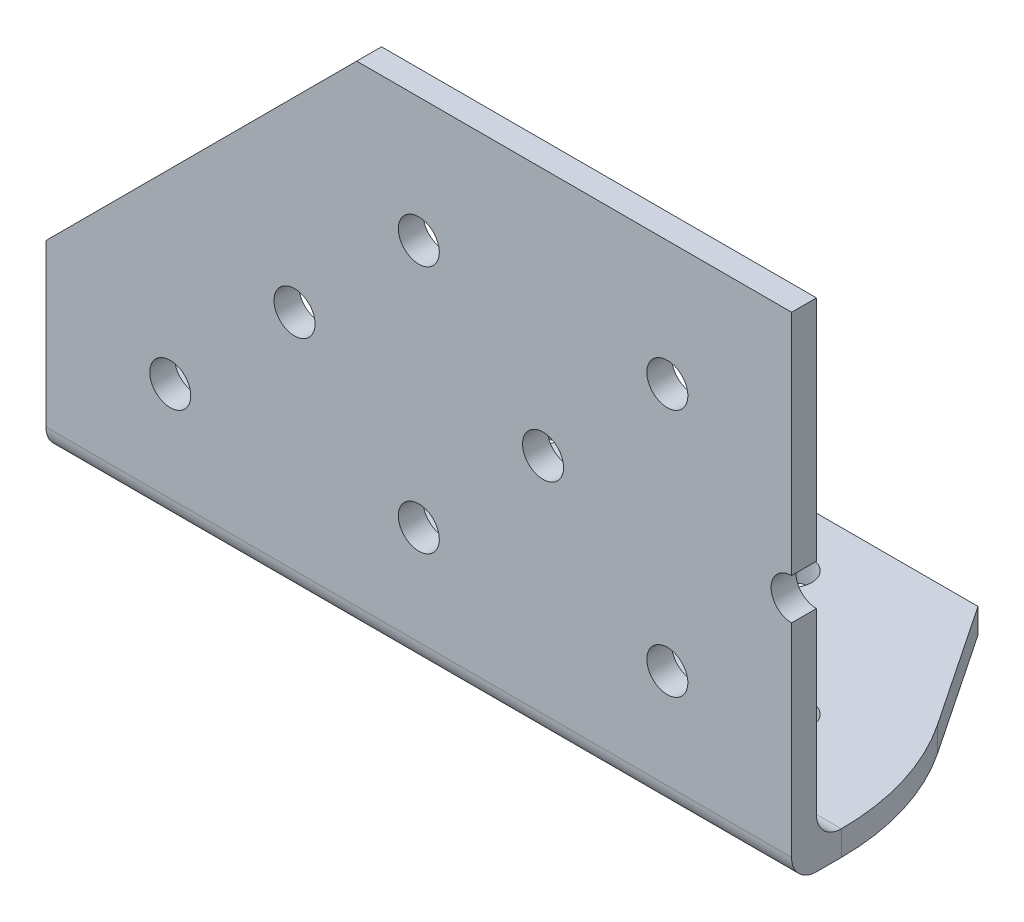
SolidWorks part; units mm, degrees
ref_plane "Front Plane" through (0, 0, 0) normal (0, 0, 1) x (1, 0, 0)
ref_plane "Top Plane" through (0, 0, 0) normal (0, 1, 0) x (1, 0, 0)
ref_plane "Right Plane" through (0, 0, 0) normal (1, 0, 0) x (0, 0, -1)
sketch "Sketch1" plane through (0, 0, 0) normal (1, 0, 0) x (0, 0, -1)
  line L0 (0, 2.54) -> (0, 50.8)
  line L1 (0, 50.8) -> (2.54, 50.8)
  line L2 (2.54, 50.8) -> (2.54, 5.08)
  line L3 (5.08, 2.54) -> (50.8, 2.54)
  line L4 (50.8, 2.54) -> (50.8, 0)
  line L5 (50.8, 0) -> (2.54, 0)
  arc A0 (0, 2.54) -> (2.54, 0) centre (2.54, 2.54) ccw
  arc A1 (5.08, 2.54) -> (2.54, 5.08) centre (5.08, 5.08) cw
  point P10 (0, 0)
  dimension "D5" = 2.54
  dimension "D6" = 2.54
  dimension "D1" = 2.54
  dimension "D2" = 2.54
  dimension "D3" = 50.8
  dimension "D4" = 50.8
extrude "Boss-Extrude1" add sketch "Sketch1" along normal blind 76.2
sketch "Sketch2" plane through (0, 2.54, 0) normal (0, 1, 0) x (1, 0, 0)
  line L0 (76.2, 50.8) -> (0, 50.8) construction
  line L1 (0, 50.8) -> (0, 5.08) construction
  line L2 (12.7, 38.0619) -> (12.7, 12.6619) construction
  line L3 (0, 25.3619) -> (5.5771, 25.3619) construction
  circle A0 centre (12.7, 38.0619) radius 2.0955
  circle A1 centre (12.7, 12.6619) radius 2.0955
  circle A2 centre (25.4, 25.3619) radius 2.0955
  point P12 (12.7, 25.3619)
  dimension "D1" = 4.191
  dimension "D2" = 4.191
  dimension "D6" = 4.191
  dimension "D3" = 12.7381
  dimension "D4" = 25.4
  dimension "D5" = 12.7
  dimension "D7" = 25.4
extrude "Cut-Extrude1" cut sketch "Sketch2" against normal through all
pattern_linear "LPattern1" count 3 spacing 25.4 along (1, 0, 0) of "Cut-Extrude1"
sketch "Sketch3" plane through (0, 0, -2.54) normal (0, 0, -1) x (-1, 0, 0)
  line L0 (-12.7, 38.1) -> (-12.7, 12.7) construction
  line L1 (-61.8614, 25.4) -> (-56.2843, 25.4) construction
  line L2 (0, 5.08) -> (0, 50.8) construction
  line L3 (-76.2, 50.8) -> (0, 50.8) construction
  circle A0 centre (-12.7, 38.1) radius 2.0955
  circle A1 centre (-12.7, 12.7) radius 2.0955
  circle A2 centre (-25.4, 25.4) radius 2.0955
  point P8 (-12.7, 25.4)
  dimension "D1" = 4.191
  dimension "D2" = 4.191
  dimension "D4" = 4.191
  dimension "D3" = 25.4
  dimension "D5" = 12.7
  dimension "D6" = 25.4
  dimension "D7" = 12.7
extrude "Cut-Extrude2" cut sketch "Sketch3" against normal through all
pattern_linear "LPattern2" count 3 spacing 25.4 along (1, 0, 0) of "Cut-Extrude2"
ref_plane "Plane1" through (39.751, 0, 0) normal (1, 0, 0) x (0, 0, -1)
sketch "Sketch4" plane through (0, 2.54, 0) normal (0, 1, 0) x (1, 0, 0)
  line L0 (0, 50.8) -> (0, 5.08) construction
  line L1 (76.2, 50.8) -> (0, 50.8)
  line L2 (76.2, 50.8) -> (76.2, 31.75)
  line L3 (76.2, 31.75) -> (0, 31.75)
  line L4 (0, 50.8) -> (0, 31.75)
  dimension "D1" = 19.05
extrude "Cut-Extrude3" cut sketch "Sketch4" against normal through all
sketch "Sketch5" plane through (0, 0, -2.54) normal (0, 0, -1) x (-1, 0, 0)
  line L0 (-38.1, 12.7) -> (-12.7, 38.1) construction
  line L1 (-76.2, 19.05) -> (-44.45, 50.8)
  line L2 (-76.2, 5.08) -> (-76.2, 23.3045) construction
  line L3 (-76.2, 50.8) -> (0, 50.8) construction
  line L4 (-76.2, 19.05) -> (-76.2, 50.8)
  line L5 (-76.2, 50.8) -> (-44.45, 50.8)
  line L6 (-38.1, 50.8) -> (-38.1, 5.08) construction
  line L7 (-76.2, 5.08) -> (0, 5.08) construction
  dimension "D1" = 31.75
extrude "Cut-Extrude4" [suppressed] cut sketch "Sketch5" against normal through all
sketch "Sketch6" plane through (0, 0, -2.54) normal (0, 0, -1) x (-1, 0, 0)
  line L0 (0, 19.05) -> (0, 50.8)
  line L1 (0, 50.8) -> (-31.75, 50.8)
  line L2 (0, 19.05) -> (-31.75, 50.8)
  dimension "D1" = 31.75
  dimension "D2" = 31.75
  dimension "D3" = 44.9013
extrude "Cut-Extrude5" cut sketch "Sketch6" against normal through all
sketch "Sketch7" plane through (0, 2.54, 0) normal (0, 1, 0) x (1, 0, 0)
  line L0 (63.5, 31.75) -> (12.7, 31.75) construction
  line L1 (0, 31.75) -> (76.2, 31.75) construction
  line L2 (63.5, 31.75) -> (71.8975, 19.224)
  line L3 (12.7, 31.75) -> (4.3025, 19.224)
  line L5 (76.2, 23.2664) -> (76.2, 5.08) construction
  line L6 (0, 31.75) -> (0, 5.08) construction
  line L7 (76.2, 5.08) -> (76.2, 31.75)
  line L8 (76.2, 31.75) -> (63.5, 31.75)
  line L9 (0, 5.08) -> (0, 31.75)
  line L10 (0, 31.75) -> (12.7, 31.75)
  arc A0 (76.2, 5.08) -> (71.8975, 19.224) centre (50.8, 5.08) ccw
  arc A1 (0, 5.08) -> (4.3025, 19.224) centre (25.4, 5.08) cw
  point P5 (38.1, 31.75)
  dimension "D2" = 25.4
  dimension "D1" = 50.8
extrude "Cut-Extrude6" cut sketch "Sketch7" against normal through all both and the other way through all
